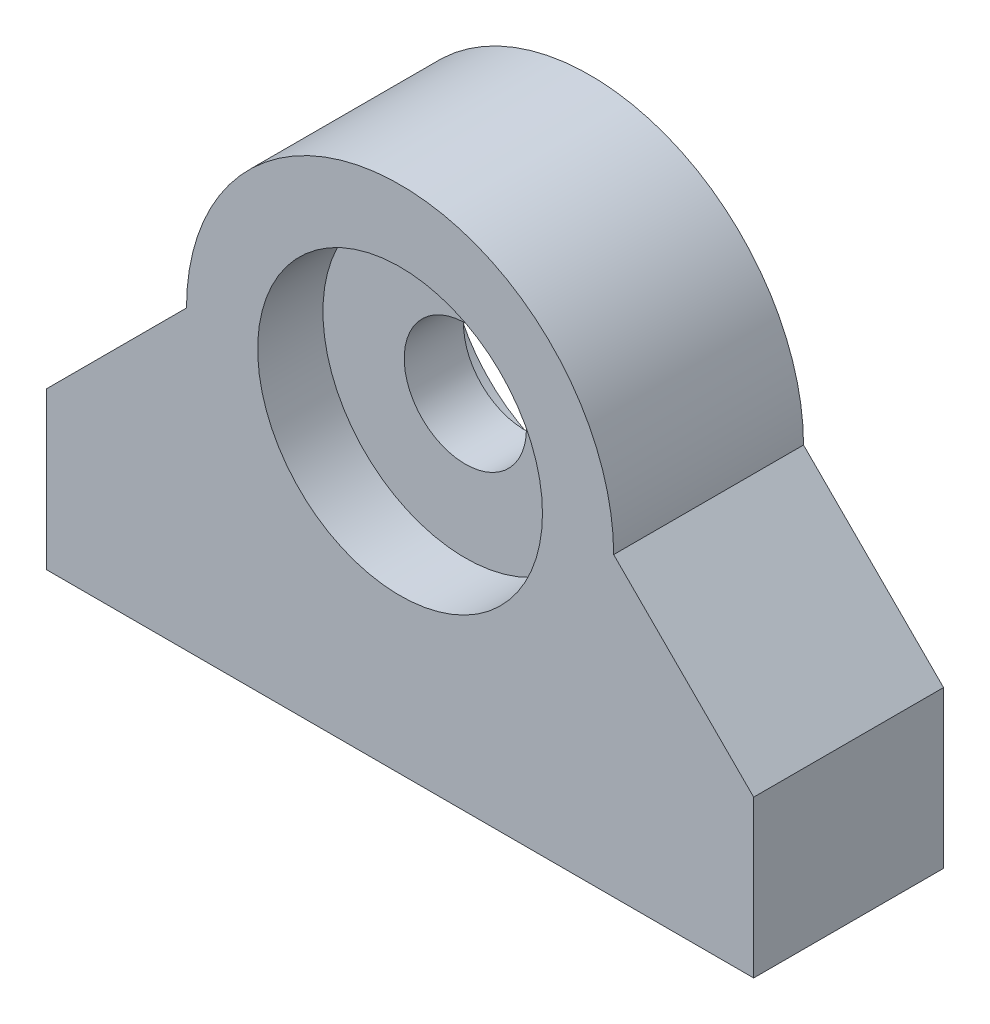
SolidWorks part; units mm, degrees
ref_plane "Front Plane" through (0, 0, 0) normal (0, 0, 1) x (1, 0, 0)
ref_plane "Top Plane" through (0, 0, 0) normal (0, 1, 0) x (1, 0, 0)
ref_plane "Right Plane" through (0, 0, 0) normal (1, 0, 0) x (0, 0, -1)
sketch "Sketch1" plane through (0, 0, 0) normal (0, 0, 1) x (1, 0, 0)
  line L0 (0, -26.1041) -> (0, 52.7781) construction
  line L3 (0, 0) -> (-18.923, 0)
  line L4 (18.923, 0) -> (18.923, 8.382)
  line L5 (18.923, 8.382) -> (11.43, 15.875)
  line L7 (-18.923, 0) -> (-18.923, 8.382)
  line L8 (0, 0) -> (18.923, 0)
  line L9 (-18.923, 8.382) -> (-11.43, 15.875)
  circle A0 centre (0, 15.875) radius 7.62
  arc A1 (-11.43, 15.875) -> (11.43, 15.875) centre (0, 15.875) cw
  point P3 (-16.51, 0)
  point P4 (0, 0)
  point P7 (-16.51, 0.1591)
  point P11 (0, 4.699)
  point P12 (0, 28.448)
  point P15 (0, 8.255)
  dimension "D6" = 15.24
  dimension "D3" = 3.81
  dimension "D4" = 45
  dimension "D5" = 15.875
  dimension "D7" = 37.846
extrude "Boss-Extrude1" add sketch "Sketch1" along normal blind 10.16
ref_plane "Plane1" through (0, 0, 5.08) normal (0, 0, 1) x (1, 0, 0)
sketch "Sketch3" plane through (0, 0, 5.08) normal (0, 0, 1) x (1, 0, 0)
  circle A0 centre (0, 15.875) radius 3.2703
  circle A1 centre (0, 15.875) radius 8.7376
  dimension "D1" = 6.5405
  dimension "D2" = 17.4752
extrude "Boss-Extrude2" add sketch "Sketch3" along normal blind 1.5875 and the other way blind 1.5875
sketch "Sketch4" plane through (0, 0, 0) normal (0, -1, 0) x (-1, 0, 0)
  line L1 (-15.0178, -5.08) -> (15.0178, -5.08) construction
  line L3 (0, 9.7586) -> (0, -18.8259) construction
  circle A0 centre (-10.16, -5.08) radius 1.9837
  circle A1 centre (10.16, -5.08) radius 1.9837
  point P0 (0, 0)
  point P2 (0, 0)
  dimension "D1" = 3.9675
  dimension "D2" = 10.16
extrude "Cut-Extrude1" cut sketch "Sketch4" against normal blind 10.16
equation "\"0.095inin\"=0.085"
